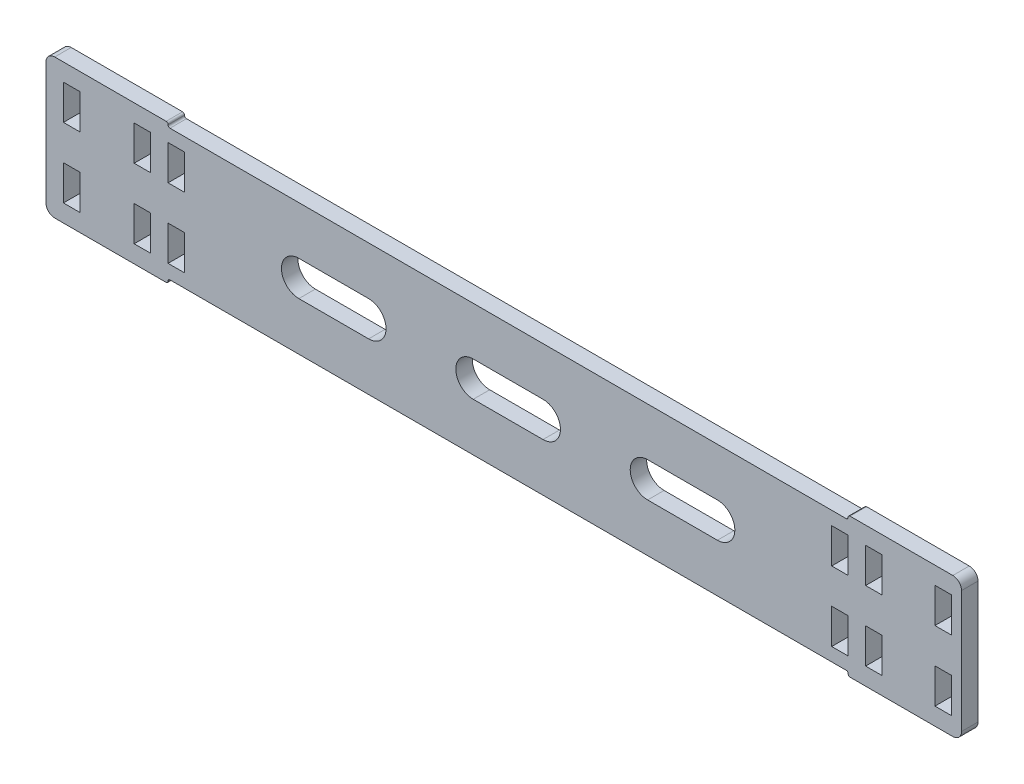
SolidWorks part; units mm, degrees
ref_plane "Front Plane" through (0, 0, 0) normal (0, 0, 1) x (1, 0, 0)
ref_plane "Top Plane" through (0, 0, 0) normal (0, 1, 0) x (1, 0, 0)
ref_plane "Right Plane" through (0, 0, 0) normal (1, 0, 0) x (0, 0, -1)
sketch "Sketch1" plane through (0, 0, 0) normal (0, 0, 1) x (1, 0, 0)
  line L0 (-18.6944, 19.05) -> (-18.6944, 6.35)
  line L1 (0, 0) -> (-304.8, 0)
  line L2 (0, 0) -> (0, 50.8)
  line L3 (0, 50.8) -> (-304.8, 50.8)
  line L4 (-304.8, 0) -> (-304.8, 50.8)
  line L5 (-18.6944, 44.45) -> (-12.7, 44.45)
  line L6 (-18.6944, 44.45) -> (-18.6944, 31.75)
  line L7 (-18.6944, 31.75) -> (-12.7, 31.75)
  line L8 (-12.7, 44.45) -> (-12.7, 31.75)
  line L9 (-18.6944, 19.05) -> (-12.7, 19.05)
  line L10 (-12.7, 19.05) -> (-12.7, 6.35)
  line L11 (-18.6944, 6.35) -> (-12.7, 6.35)
  line L12 (-260.35, 31.75) -> (-254.3556, 31.75)
  line L13 (-260.35, 44.45) -> (-260.35, 31.75)
  line L14 (-260.35, 44.45) -> (-254.3556, 44.45)
  line L15 (-254.3556, 44.45) -> (-254.3556, 31.75)
  line L16 (-260.35, 19.05) -> (-254.3556, 19.05)
  line L17 (-260.35, 19.05) -> (-260.35, 6.35)
  line L18 (-260.35, 6.35) -> (-254.3556, 6.35)
  line L19 (-254.3556, 19.05) -> (-254.3556, 6.35)
  line L20 (-292.4556, 19.05) -> (-292.4556, 6.35)
  line L21 (-298.45, 6.35) -> (-292.4556, 6.35)
  line L22 (-298.45, 19.05) -> (-298.45, 6.35)
  line L23 (-298.45, 19.05) -> (-292.4556, 19.05)
  line L24 (-298.45, 31.75) -> (-292.4556, 31.75)
  line L25 (-298.45, 44.45) -> (-298.45, 31.75)
  line L26 (-298.45, 44.45) -> (-292.4556, 44.45)
  line L27 (-292.4556, 44.45) -> (-292.4556, 31.75)
  dimension "D1" = 50.8
  dimension "D2" = 304.8
  dimension "D3" = 5.9944
  dimension "D4" = 12.7
  dimension "D5" = 6.35
  dimension "D7" = 12.7
  dimension "D9" = 44.45
  dimension "D6" = 2
  dimension "D8" = 2
  dimension "D10" = 2
extrude "Boss-Extrude1" add sketch "Sketch1" along normal blind 5.9944
sketch "Sketch3" plane through (0, 0, 5.9944) normal (0, 0, 1) x (1, 0, 0)
  line L0 (0, 50.8) -> (-304.8, 50.8) construction
  line L1 (-260.35, 50.8) -> (-12.7, 50.8)
  line L2 (-260.35, 50.8) -> (-260.35, 49.3125)
  line L3 (-260.35, 49.3125) -> (-12.7, 49.3125)
  line L4 (-12.7, 50.8) -> (-12.7, 49.3125)
  line L7 (-260.35, 44.45) -> (-260.35, 31.75) construction
  line L8 (-12.7, 31.75) -> (-12.7, 44.45) construction
  line L9 (-304.8, 25.4) -> (0, 25.4) construction
  line L10 (-304.8, 50.8) -> (-304.8, 0) construction
  line L11 (0, 0) -> (0, 50.8) construction
  line L12 (-12.7, 0) -> (-12.7, 1.4875)
  line L13 (-260.35, 1.4875) -> (-12.7, 1.4875)
  line L14 (-260.35, 0) -> (-260.35, 1.4875)
  line L15 (-260.35, 0) -> (-12.7, 0)
  dimension "D1" = 1.4875
extrude "Cut-Extrude3" cut sketch "Sketch3" against normal through all
fillet "Fillet4" radius 0.7 8 edges at (-12.7, 50.8, 2.9972) (-12.7, 49.3125, 2.9972) (-260.35, 50.8, 2.9972) (-260.35, 49.3125, 2.9972) (-260.35, 0, 2.9972) (-260.35, 1.4875, 2.9972) (-12.7, 0, 2.9972) (-12.7, 1.4875, 2.9972)
sketch "Sketch4" plane through (0, 0, 5.9944) normal (0, 0, 1) x (1, 0, 0)
  line L1 (0, 50.8) -> (28.575, 50.8)
  line L2 (0, 50.8) -> (0, 0)
  line L3 (0, 0) -> (28.575, 0)
  line L4 (28.575, 50.8) -> (28.575, 0)
  dimension "D1" = 28.575
extrude "Boss-Extrude2" add sketch "Sketch4" against normal up to surface (5.9944 mm away) up to face at (-139.7, 25.4, 0)
sketch "Sketch5" plane through (0, 0, 5.9944) normal (0, 0, 1) x (1, 0, 0)
  line L0 (-12.7, 44.45) -> (28.575, 44.45) construction
  line L1 (28.575, 0) -> (28.575, 50.8) construction
  line L2 (-12.7, 6.35) -> (28.575, 6.35) construction
  line L3 (-12.7, 6.35) -> (-12.7, 19.05) construction
  line L4 (-18.6944, 6.35) -> (-12.7, 6.35) construction
  line L5 (-12.7, 19.05) -> (28.575, 19.05) construction
  line L6 (-12.7, 31.75) -> (28.575, 31.75) construction
  line L8 (18.8961, 44.45) -> (24.8905, 44.45)
  line L9 (18.8961, 44.45) -> (18.8961, 31.75)
  line L10 (18.8961, 31.75) -> (24.8905, 31.75)
  line L11 (24.8905, 44.45) -> (24.8905, 31.75)
  line L12 (18.8961, 19.05) -> (24.8905, 19.05)
  line L13 (18.8961, 19.05) -> (18.8961, 6.35)
  line L14 (18.8961, 6.35) -> (24.8905, 6.35)
  line L15 (24.8905, 19.05) -> (24.8905, 6.35)
  dimension "D1" = 5.9944
  dimension "D2" = 5.9944
  dimension "D3" = 3.6845
  dimension "D4" = 3.6845
extrude "Cut-Extrude4" cut sketch "Sketch5" against normal through all
fillet "Fillet5" radius 3.175 4 edges at (-304.8, 50.8, 2.9972) (-304.8, 0, 2.9972) (28.575, 0, 2.9972) (28.575, 50.8, 2.9972)
sketch "Sketch6" plane through (0, 0, 5.9944) normal (0, 0, 1) x (1, 0, 0)
  line L0 (-136.525, 49.3125) -> (-136.525, 1.4875) construction
  line L1 (-259.65, 49.3125) -> (-13.4, 49.3125) construction
  line L2 (-13.4, 1.4875) -> (-259.65, 1.4875) construction
  line L3 (-123.825, 25.4) -> (-149.225, 25.4) construction
  line L4 (-123.825, 19.05) -> (-149.225, 19.05)
  line L5 (-123.825, 31.75) -> (-149.225, 31.75)
  line L6 (-60.325, 25.4) -> (-85.725, 25.4) construction
  line L7 (-60.325, 19.05) -> (-85.725, 19.05)
  line L8 (-60.325, 31.75) -> (-85.725, 31.75)
  line L9 (-187.325, 25.4) -> (-212.725, 25.4) construction
  line L10 (-187.325, 19.05) -> (-212.725, 19.05)
  line L11 (-187.325, 31.75) -> (-212.725, 31.75)
  arc A0 (-123.825, 19.05) -> (-123.825, 31.75) centre (-123.825, 25.4) ccw
  arc A1 (-149.225, 31.75) -> (-149.225, 19.05) centre (-149.225, 25.4) ccw
  arc A2 (-60.325, 19.05) -> (-60.325, 31.75) centre (-60.325, 25.4) ccw
  arc A3 (-85.725, 31.75) -> (-85.725, 19.05) centre (-85.725, 25.4) ccw
  arc A4 (-187.325, 19.05) -> (-187.325, 31.75) centre (-187.325, 25.4) ccw
  arc A5 (-212.725, 31.75) -> (-212.725, 19.05) centre (-212.725, 25.4) ccw
  point P8 (-136.525, 25.4)
  point P16 (-73.025, 25.4)
  point P23 (-200.025, 25.4)
  dimension "D2" = 6.35
  dimension "D1" = 25.4
  dimension "D3" = 2
  dimension "D4" = 2
extrude "Cut-Extrude5" cut sketch "Sketch6" against normal through all
sketch "Sketch7" plane through (0, 0, 5.9944) normal (0, 0, 1) x (1, 0, 0)
  line L0 (-136.525, 49.3125) -> (-136.525, 1.4875) construction
  line L1 (-259.65, 49.3125) -> (-13.4, 49.3125) construction
  line L2 (-13.4, 1.4875) -> (-259.65, 1.4875) construction
  line L3 (-292.4556, 44.45) -> (-260.35, 44.45) construction
  line L4 (-260.35, 6.35) -> (-292.4556, 6.35) construction
  line L5 (-298.45, 6.35) -> (-292.4556, 6.35) construction
  line L6 (-292.4556, 31.75) -> (-260.35, 31.75) construction
  line L7 (-260.35, 19.05) -> (-292.4556, 19.05) construction
  line L8 (-260.35, 44.45) -> (-260.35, 31.75) construction
  line L9 (-272.6944, 44.45) -> (-266.7, 44.45)
  line L10 (-272.6944, 44.45) -> (-272.6944, 31.75)
  line L11 (-272.6944, 31.75) -> (-266.7, 31.75)
  line L12 (-266.7, 44.45) -> (-266.7, 31.75)
  line L13 (-6.35, 44.45) -> (-6.35, 31.75)
  line L14 (-272.6944, 19.05) -> (-266.7, 19.05)
  line L15 (-272.6944, 19.05) -> (-272.6944, 6.35)
  line L16 (-272.6944, 6.35) -> (-266.7, 6.35)
  line L17 (-266.7, 19.05) -> (-266.7, 6.35)
  line L18 (-0.3556, 31.75) -> (-6.35, 31.75)
  line L19 (-0.3556, 44.45) -> (-0.3556, 31.75)
  line L20 (-0.3556, 44.45) -> (-6.35, 44.45)
  line L21 (-0.3556, 6.35) -> (-6.35, 6.35)
  line L22 (-6.35, 19.05) -> (-6.35, 6.35)
  line L23 (-0.3556, 19.05) -> (-6.35, 19.05)
  line L24 (-0.3556, 19.05) -> (-0.3556, 6.35)
  dimension "D1" = 5.9944
  dimension "D2" = 6.35
extrude "Cut-Extrude6" cut sketch "Sketch7" against normal through all
